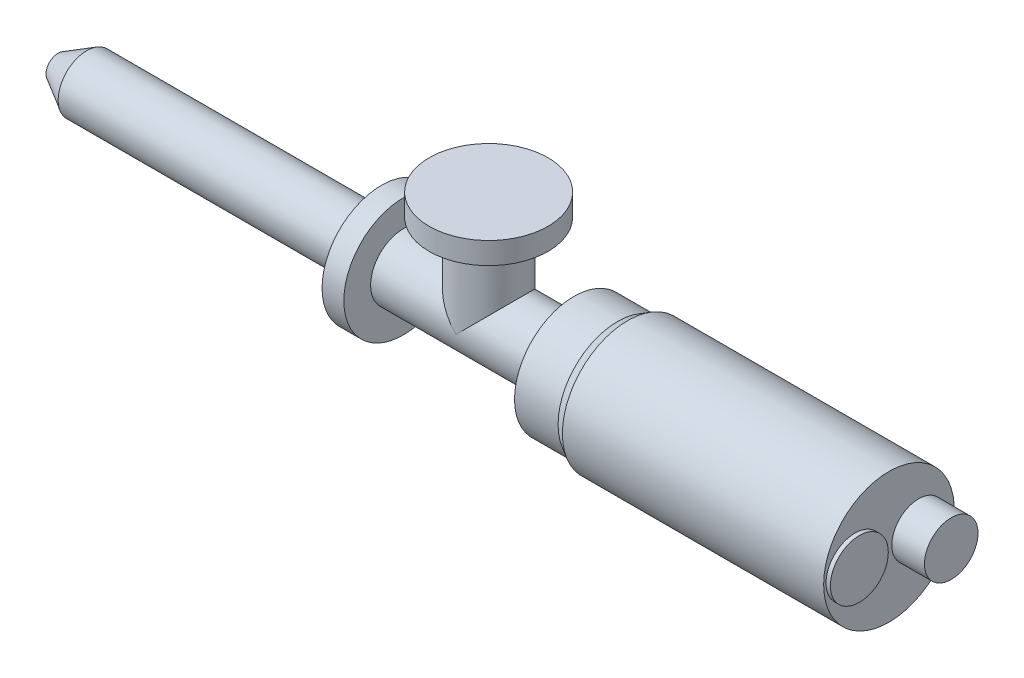
SolidWorks part; units mm, degrees
ref_plane "Front Plane" through (0, 0, 0) normal (0, 0, 1) x (1, 0, 0)
ref_plane "Top Plane" through (0, 0, 0) normal (0, 1, 0) x (1, 0, 0)
ref_plane "Right Plane" through (0, 0, 0) normal (1, 0, 0) x (0, 0, -1)
sketch "Sketch1" plane through (0, 0, 0) normal (0, 0, 1) x (1, 0, 0)
  line L0 (0, 0) -> (1031.9175, 0) construction
  line L1 (0, 0) -> (0, 6.985)
  line L2 (0, 6.985) -> (16.7617, 16.6624)
  line L3 (16.7617, 16.6624) -> (188.722, 16.6624)
  line L4 (188.722, 16.6624) -> (188.722, 34.671)
  line L5 (188.722, 34.671) -> (201.422, 34.671)
  line L6 (201.422, 34.671) -> (201.422, 19.05)
  line L7 (201.422, 19.05) -> (300.99, 19.05)
  line L8 (300.99, 19.05) -> (300.99, 34.671)
  line L9 (300.99, 34.671) -> (326.39, 34.671)
  line L10 (326.39, 34.671) -> (332.3292, 38.1)
  line L11 (332.3292, 38.1) -> (484.7292, 38.1)
  line L12 (484.7292, 38.1) -> (484.7292, 0)
  line L13 (0, 0) -> (484.7292, 0)
  dimension "D1" = 6.985
  dimension "D2" = 30
  dimension "D3" = 16.6624
  dimension "D4" = 188.722
  dimension "D5" = 12.7
  dimension "D6" = 34.671
  dimension "D7" = 99.568
  dimension "D8" = 25.4
  dimension "D9" = 34.671
  dimension "D10" = 30
  dimension "D11" = 38.1
  dimension "D12" = 152.4
  dimension "D13" = 19.05
revolve "Revolve1" add sketch "Sketch1" angle 360 about L0
sketch "Sketch2" plane through (0, 0, 0) normal (0, 1, 0) x (1, 0, 0)
  line L0 (188.722, 34.671) -> (188.722, -34.671) construction
  circle A0 centre (251.206, 0) radius 19.05
  dimension "D1" = 38.1
  dimension "D2" = 62.484
extrude "Boss-Extrude1" add sketch "Sketch2" along normal blind 62.484
sketch "Sketch3" plane through (0, 62.484, 0) normal (0, 1, 0) x (1, 0, 0)
  circle A0 centre (251.206, 0) radius 34.671
  dimension "D1" = 69.342
extrude "Boss-Extrude2" add sketch "Sketch3" against normal blind 12.7
sketch "Sketch4" plane through (484.7292, 0, 0) normal (1, 0, 0) x (0, 0, -1)
  circle A0 centre (17.272, 0) radius 15.621
  dimension "D1" = 31.242
  dimension "D2" = 0
  dimension "D3" = 17.272
extrude "Boss-Extrude3" add sketch "Sketch4" along normal blind 19.05
sketch "Sketch5" plane through (484.7292, 0, 0) normal (1, 0, 0) x (0, 0, -1)
  circle A0 centre (-19.812, 0) radius 16.891
  dimension "D2" = 33.782
  dimension "D1" = 0
  dimension "D3" = 19.812
extrude "Boss-Extrude4" add sketch "Sketch5" along normal blind 2.54
